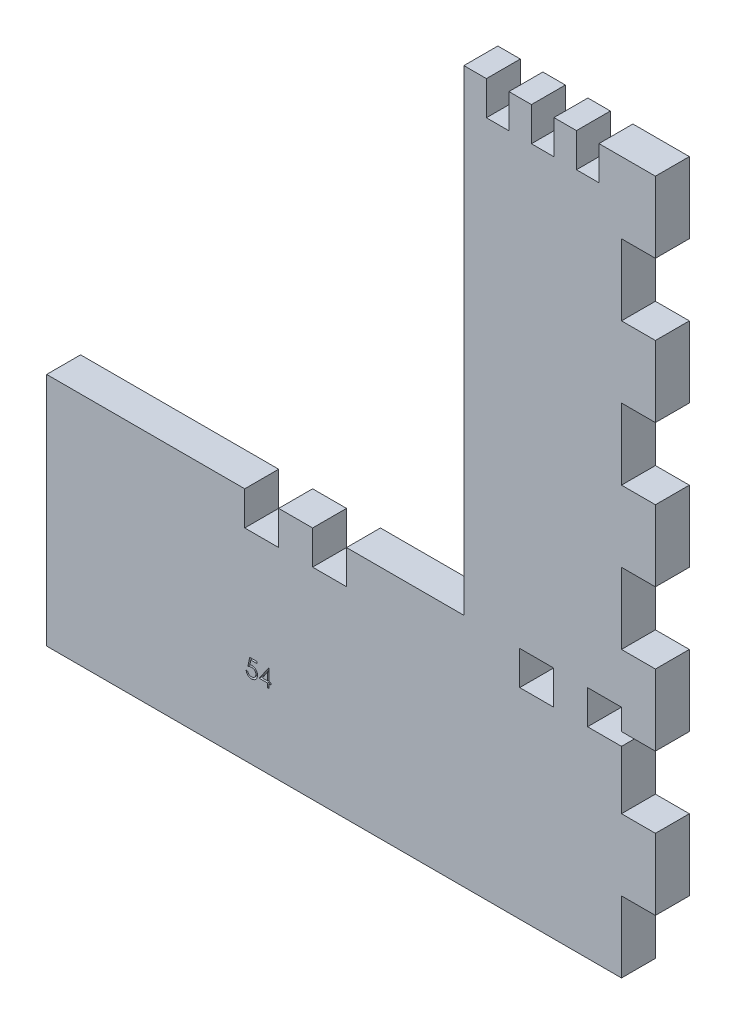
SolidWorks part; units mm, degrees
material "Acrylic (Medium-high impact)"
ref_plane "Front Plane" through (0, 0, 0) normal (0, 0, 1) x (1, 0, 0)
ref_plane "Top Plane" through (0, 0, 0) normal (0, 1, 0) x (1, 0, 0)
ref_plane "Right Plane" through (0, 0, 0) normal (1, 0, 0) x (0, 0, -1)
sketch "Sketch6" plane through (0, 0, 0) normal (0, 0, 1) x (1, 0, 0)
  line L5 (107.544, 124.7925) -> (188.794, 124.7925)
  line L6 (107.544, 124.7925) -> (107.544, -5.2075)
  line L7 (107.544, -5.2075) -> (188.794, -5.2075)
  line L8 (188.794, 124.7925) -> (188.794, -5.2075)
  line L9 (107.544, 124.7925) -> (153.794, 124.7925)
  line L10 (107.544, 124.7925) -> (107.544, 37.7925)
  line L11 (107.544, 37.7925) -> (153.794, 37.7925)
  line L12 (153.794, 124.7925) -> (153.794, 37.7925)
  line L13 (113.744, 37.7925) -> (119.944, 37.7925)
  line L14 (113.744, 37.7925) -> (113.744, 31.5925)
  line L15 (113.744, 31.5925) -> (119.944, 31.5925)
  line L16 (119.944, 37.7925) -> (119.944, 31.5925)
  line L17 (107.544, 37.7925) -> (77.544, 37.7925)
  line L18 (126.144, 37.7925) -> (132.344, 37.7925)
  line L19 (126.144, 37.7925) -> (126.144, 31.5925)
  line L20 (126.144, 31.5925) -> (132.344, 31.5925)
  line L21 (132.344, 37.7925) -> (132.344, 31.5925)
  line L26 (188.794, 111.7925) -> (182.594, 111.7925)
  line L27 (188.794, 111.7925) -> (188.794, 98.7925)
  line L28 (188.794, 98.7925) -> (182.594, 98.7925)
  line L29 (182.594, 111.7925) -> (182.594, 98.7925)
  line L30 (188.794, 85.7925) -> (182.594, 85.7925)
  line L31 (188.794, 85.7925) -> (188.794, 72.7925)
  line L32 (188.794, 72.7925) -> (182.594, 72.7925)
  line L33 (182.594, 85.7925) -> (182.594, 72.7925)
  line L34 (188.794, 59.7925) -> (182.594, 59.7925)
  line L35 (188.794, 59.7925) -> (188.794, 46.7925)
  line L36 (188.794, 46.7925) -> (182.594, 46.7925)
  line L37 (182.594, 59.7925) -> (182.594, 46.7925)
  line L42 (188.794, 33.7925) -> (182.594, 33.7925)
  line L43 (188.794, 33.7925) -> (188.794, 20.7925)
  line L44 (188.794, 20.7925) -> (182.594, 20.7925)
  line L45 (182.594, 33.7925) -> (182.594, 20.7925)
  line L46 (188.794, 7.7925) -> (182.594, 7.7925)
  line L47 (188.794, 7.7925) -> (188.794, -5.2075)
  line L48 (188.794, -5.2075) -> (182.594, -5.2075)
  line L49 (182.594, 7.7925) -> (182.594, -5.2075)
  line L50 (157.908, 124.7925) -> (162.022, 124.7925)
  line L51 (157.908, 124.7925) -> (157.908, 118.5925)
  line L52 (157.908, 118.5925) -> (162.022, 118.5925)
  line L53 (162.022, 124.7925) -> (162.022, 118.5925)
  line L54 (166.136, 124.7925) -> (170.25, 124.7925)
  line L55 (166.136, 124.7925) -> (166.136, 118.5925)
  line L56 (166.136, 118.5925) -> (170.25, 118.5925)
  line L57 (170.25, 124.7925) -> (170.25, 118.5925)
  line L58 (174.364, 124.7925) -> (178.478, 124.7925)
  line L59 (174.364, 124.7925) -> (174.364, 118.5925)
  line L60 (174.364, 118.5925) -> (178.478, 118.5925)
  line L61 (178.478, 124.7925) -> (178.478, 118.5925)
  line L62 (182.594, 37.6539) -> (176.394, 37.6539)
  line L63 (182.594, 37.6539) -> (182.594, 31.4539)
  line L64 (182.594, 31.4539) -> (176.394, 31.4539)
  line L65 (176.394, 37.6539) -> (176.394, 31.4539)
  line L66 (170.194, 37.6539) -> (163.994, 37.6539)
  line L67 (170.194, 37.6539) -> (170.194, 31.4539)
  line L68 (170.194, 31.4539) -> (163.994, 31.4539)
  line L69 (163.994, 37.6539) -> (163.994, 31.4539)
  line L70 (107.544, 37.7925) -> (107.544, -5.2075)
  line L71 (107.544, -5.2075) -> (77.544, -5.2075)
  line L72 (77.544, 37.7925) -> (77.544, -5.2075)
  dimension "D1" = 81.25
  dimension "D2" = 130
  dimension "D3" = 87
  dimension "D4" = 46.25
  dimension "D5" = 6.2
  dimension "D6" = 6.2
  dimension "D7" = 6.2
  dimension "D8" = 6.2
  dimension "D9" = 6.2
  dimension "D10" = 6.2
  dimension "D11" = 13
  dimension "D12" = 6.2
  dimension "D13" = 13
  dimension "D14" = 13
  dimension "D15" = 6.2
  dimension "D16" = 13
  dimension "D17" = 13
  dimension "D18" = 6.2
  dimension "D19" = 13
  dimension "D20" = 6.2
  dimension "D21" = 13
  dimension "D22" = 13
  dimension "D23" = 13
  dimension "D24" = 6.2
  dimension "D25" = 4.114
  dimension "D26" = 4.114
  dimension "D27" = 4.114
  dimension "D28" = 6.2
  dimension "D29" = 6.2
  dimension "D30" = 4.114
  dimension "D31" = 4.114
  dimension "D32" = 6.2
  dimension "D33" = 4.114
  dimension "D34" = 6.2
  dimension "D35" = 6.2
  dimension "D36" = 6.2
  dimension "D37" = 6.2
  dimension "D38" = 6.2
  dimension "D39" = 30
extrude "Boss-Extrude4" add sketch "Sketch6" along normal blind 6.2 contours L65 L62 L63 L42 L8 L36 L37 L34 L32 L33 L30 L28 L29 L26 L5 L61 L60 L59 L57 L56 L55 L53 L52 L51 L12 L11 L21 L20 L19 L16 L15 L14 L6 L7 L49 L46 L44 L45 L64 L69 L66 | L70 L17 L72 L71
sketch "Sketch7" plane through (0, 0, 6.2) normal (0, 0, 1) x (1, 0, 0)
  text T0 "54\r\n"
extrude "Cut-Extrude3" cut sketch "Sketch7" against normal blind 1
